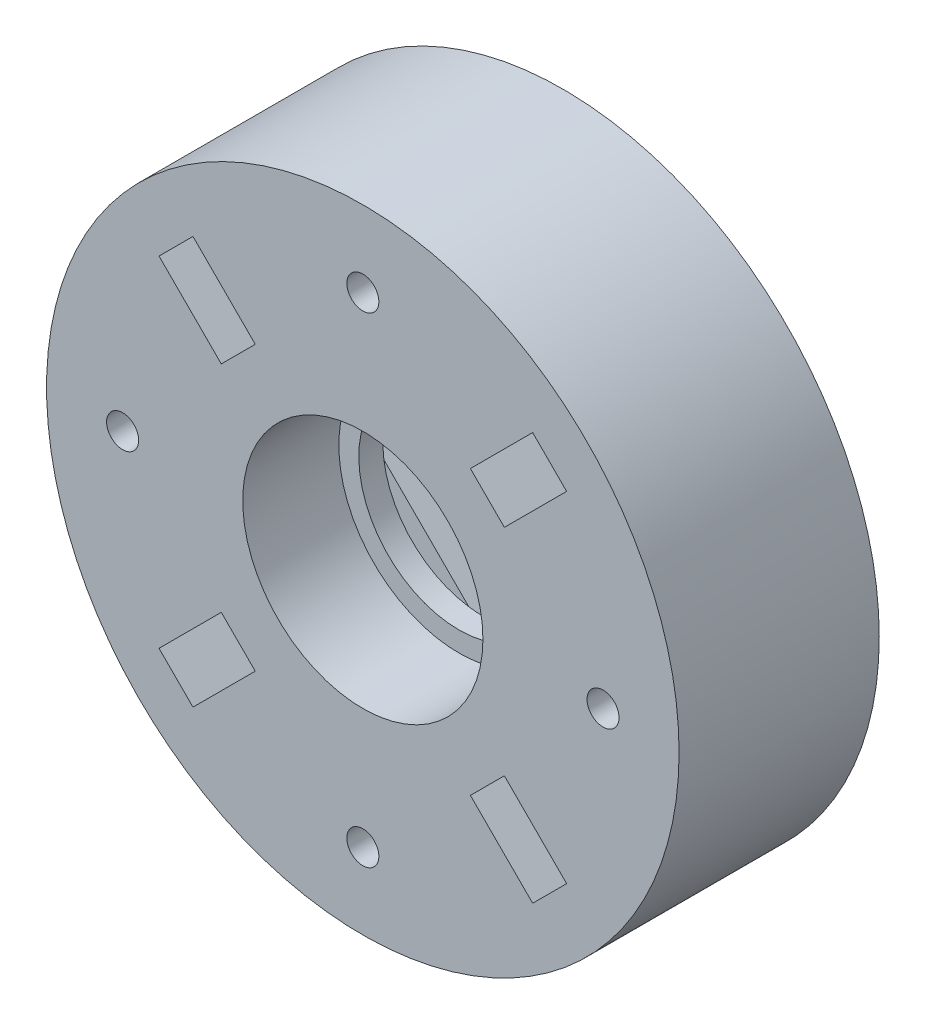
SolidWorks part; units mm, degrees
ref_plane "Alzado" through (0, 0, 0) normal (0, 0, 1) x (1, 0, 0)
ref_plane "Planta" through (0, 0, 0) normal (0, 1, 0) x (1, 0, 0)
ref_plane "Vista lateral" through (0, 0, 0) normal (1, 0, 0) x (0, 0, -1)
sketch "Croquis1" plane through (0, 0, 0) normal (0, 0, 1) x (1, 0, 0)
  line L0 (0, 50.6458) -> (0, -51.1293) construction
  circle A0 centre (0, 0) radius 39.5
  circle A1 centre (0, 0) radius 12.5
  circle A2 centre (0, 30) radius 2
  circle A3 centre (30, 0) radius 2
  circle A4 centre (0, -30) radius 2
  circle A5 centre (-30, 0) radius 2
  point P17 (0, 0)
  dimension "D1" = 79
  dimension "D2" = 25
  dimension "D4" = 4
  dimension "D3" = 30
  dimension "D5" = 4
extrude "Saliente-Extruir1" add sketch "Croquis1" along normal blind 25
sketch "Croquis3" plane through (0, 0, 25) normal (0, 0, 1) x (1, 0, 0)
  line L0 (10.6066, 10.6066) -> (28.2843, 28.2843) construction
  line L1 (0, 0) -> (39.5, 0) construction
  line L2 (17.6777, 13.435) -> (25.4558, 21.2132)
  line L3 (17.6777, 13.435) -> (13.435, 17.6777)
  line L4 (25.4558, 21.2132) -> (21.2132, 25.4558)
  line L5 (13.435, 17.6777) -> (21.2132, 25.4558)
  line L6 (17.6777, 13.435) -> (21.2132, 25.4558) construction
  line L7 (25.4558, 21.2132) -> (13.435, 17.6777) construction
  line L20 (13.435, -17.6777) -> (21.2132, -25.4558)
  line L21 (13.435, -17.6777) -> (17.6777, -13.435)
  line L22 (17.6777, -13.435) -> (25.4558, -21.2132)
  line L23 (21.2132, -25.4558) -> (25.4558, -21.2132)
  line L24 (-17.6777, -13.435) -> (-25.4558, -21.2132)
  line L25 (-17.6777, -13.435) -> (-13.435, -17.6777)
  line L26 (-13.435, -17.6777) -> (-21.2132, -25.4558)
  line L27 (-25.4558, -21.2132) -> (-21.2132, -25.4558)
  line L28 (-13.435, 17.6777) -> (-21.2132, 25.4558)
  line L29 (-13.435, 17.6777) -> (-17.6777, 13.435)
  line L30 (-17.6777, 13.435) -> (-25.4558, 21.2132)
  line L31 (-21.2132, 25.4558) -> (-25.4558, 21.2132)
  circle A0 centre (0, 0) radius 39.5 construction
  circle A1 centre (0, 0) radius 15
  point P8 (19.4454, 19.4454)
  point P27 (0.3536, 0.3536)
  point P30 (0, 0)
  dimension "D9" = 30
  dimension "D1" = 40
  dimension "D2" = 45
  dimension "D3" = 3
  dimension "D4" = 3
  dimension "D5" = 11
  dimension "D6" = 27.5
  dimension "D7" = 6
  dimension "D8" = 4
extrude "Cortar-Extruir1" cut sketch "Croquis3" against normal blind 12
sketch "Croquis5" plane through (0, 0, 0) normal (0, 0, -1) x (-1, 0, 0)
  circle A0 centre (0, 0) radius 16.8579
  dimension "D1" = 33.7158
extrude "Saliente-Extruir2" add sketch "Croquis5" against normal blind 10
sketch "Croquis4" plane through (0, 0, 0) normal (0, 0, -1) x (-1, 0, 0)
  line L0 (30, -3.5) -> (33.0311, -1.75)
  line L1 (3.5, 30) -> (1.75, 33.0311)
  line L2 (1.75, 33.0311) -> (-1.75, 33.0311)
  line L3 (-1.75, 33.0311) -> (-3.5, 30)
  line L4 (-3.5, 30) -> (-1.75, 26.9689)
  line L5 (-1.75, 26.9689) -> (1.75, 26.9689)
  line L6 (1.75, 26.9689) -> (3.5, 30)
  line L7 (33.0311, -1.75) -> (33.0311, 1.75)
  line L8 (33.0311, 1.75) -> (30, 3.5)
  line L9 (30, 3.5) -> (26.9689, 1.75)
  line L10 (26.9689, 1.75) -> (26.9689, -1.75)
  line L11 (26.9689, -1.75) -> (30, -3.5)
  line L12 (-3.5, -30) -> (-1.75, -33.0311)
  line L13 (-1.75, -33.0311) -> (1.75, -33.0311)
  line L14 (1.75, -33.0311) -> (3.5, -30)
  line L15 (3.5, -30) -> (1.75, -26.9689)
  line L16 (1.75, -26.9689) -> (-1.75, -26.9689)
  line L17 (-1.75, -26.9689) -> (-3.5, -30)
  line L18 (-30, 3.5) -> (-33.0311, 1.75)
  line L19 (-33.0311, 1.75) -> (-33.0311, -1.75)
  line L20 (-33.0311, -1.75) -> (-30, -3.5)
  line L21 (-30, -3.5) -> (-26.9689, -1.75)
  line L22 (-26.9689, -1.75) -> (-26.9689, 1.75)
  line L23 (-26.9689, 1.75) -> (-30, 3.5)
  line L24 (0, 0) -> (28.2843, 28.2843) construction
  line L25 (0, 0) -> (39.5, 0) construction
  line L26 (0.3536, -13.7886) -> (29.3449, 15.2028)
  line L27 (0.3536, -13.7886) -> (-13.7886, 0.3536)
  line L28 (29.3449, 15.2028) -> (15.2028, 29.3449)
  line L29 (-13.7886, 0.3536) -> (15.2028, 29.3449)
  line L30 (0.3536, -13.7886) -> (15.2028, 29.3449) construction
  line L31 (29.3449, 15.2028) -> (-13.7886, 0.3536) construction
  line L32 (25.1023, 25.1023) -> (18.7383, 31.4663) construction
  line L33 (25.1023, 25.1023) -> (28.9736, 21.231) construction
  line L34 (0, 0) -> (-15.8104, -15.8104) construction
  line L35 (-9.5459, -9.5459) -> (-4.5375, -14.5544) construction
  line L36 (-9.5459, -9.5459) -> (-14.3054, -4.7865) construction
  line L37 (21.9203, 28.2843) -> (-17.5609, -11.1969) construction
  line L38 (28.2843, 21.9203) -> (-9.2053, -15.5692) construction
  circle A0 centre (0, 30) radius 3.5 construction
  circle A1 centre (0, 0) radius 39.5 construction
  circle A3 centre (-12.7279, -6.364) radius 1.5
  circle A4 centre (-6.364, -12.7279) radius 1.5
  circle A5 centre (21.9203, 28.2843) radius 1.5
  circle A6 centre (28.2843, 21.9203) radius 1.5
  point P30 (0, 0)
  point P36 (7.7782, 7.7782)
  dimension "D11" = 3
  dimension "D12" = 3
  dimension "D13" = 3
  dimension "D14" = 3
  dimension "D1" = 4
  dimension "D2" = 40
  dimension "D3" = 45
  dimension "D4" = 20
  dimension "D5" = 10
  dimension "D6" = 9.5
  dimension "D7" = 4.5
  dimension "D8" = 4.5
  dimension "D9" = 4
  dimension "D10" = 4
  dimension "D15" = 41
extrude "Cortar-Extruir2" cut sketch "Croquis4" against normal blind 10
sketch "Croquis6" plane through (0, 0, 0) normal (0, 0, -1) x (-1, 0, 0)
  circle A0 centre (-12.7279, -6.364) radius 1.5
  circle A1 centre (-6.364, -12.7279) radius 1.5
  circle A2 centre (21.9203, 28.2843) radius 1.5
  circle A3 centre (28.2843, 21.9203) radius 1.5
extrude "Cortar-Extruir3" cut sketch "Croquis6" against normal blind 12
